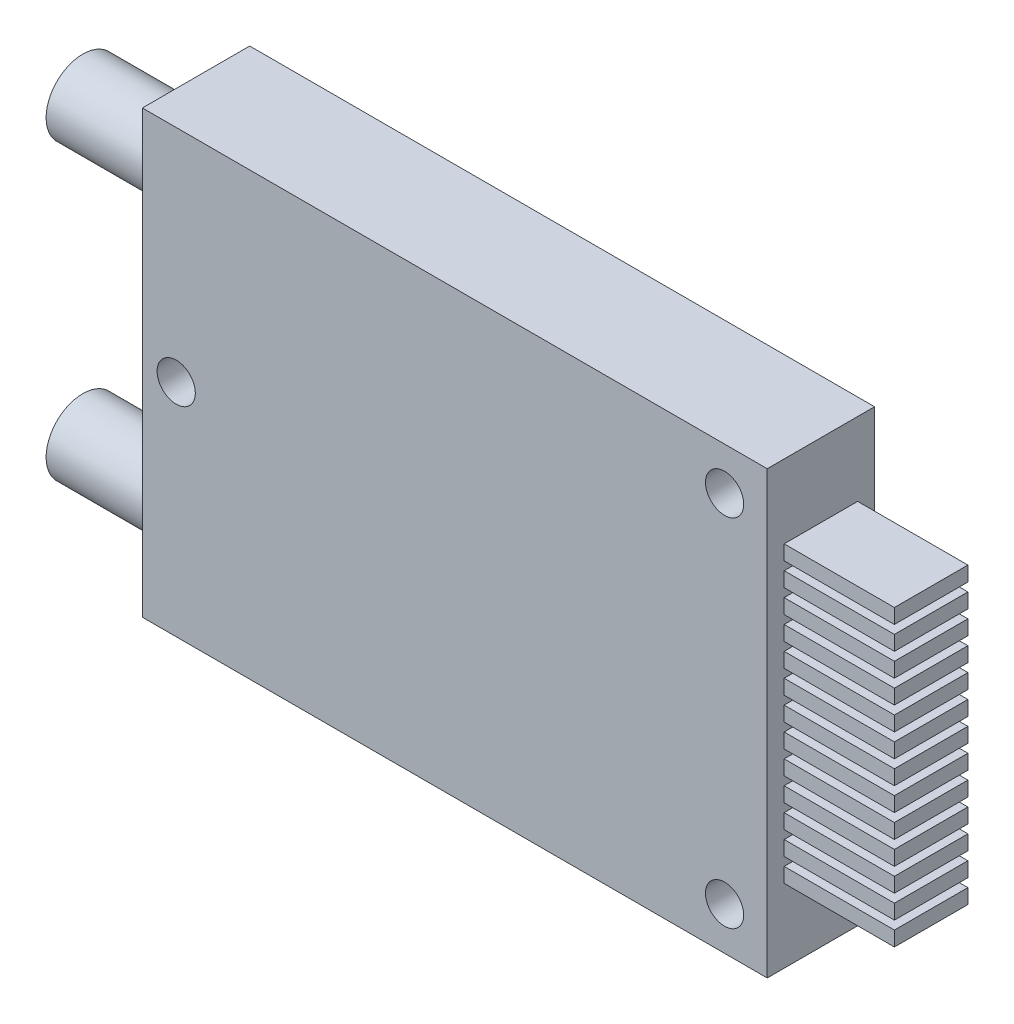
SolidWorks part; units mm, degrees
ref_plane "Front Plane" through (0, 0, 0) normal (0, 0, 1) x (1, 0, 0)
ref_plane "Top Plane" through (0, 0, 0) normal (0, 1, 0) x (1, 0, 0)
ref_plane "Right Plane" through (0, 0, 0) normal (1, 0, 0) x (0, 0, -1)
sketch "Sketch1" plane through (0, 0, 0) normal (0, 0, 1) x (1, 0, 0)
  line L1 (-21.25, 15) -> (21.25, 15)
  line L2 (-21.25, 15) -> (-21.25, -15)
  line L3 (-21.25, -15) -> (21.25, -15)
  line L4 (21.25, 15) -> (21.25, -15)
  point P4 (0, -15)
  point P5 (21.25, 0)
  dimension "D1" = 42.5
  dimension "D2" = 30
extrude "Boss-Extrude1" add sketch "Sketch1" along normal blind 7.3 contours L2 L3 L4 L1
sketch "Sketch2" plane through (0, 0, 7.3) normal (0, 0, 1) x (1, 0, 0)
  line L0 (-21.25, 15) -> (21.25, 15) construction
  line L1 (21.25, 15) -> (21.25, -15) construction
  line L2 (-21.25, -15) -> (21.25, -15) construction
  line L3 (-21.25, 15) -> (-21.25, -15) construction
  circle A0 centre (18.35, -12.1) radius 1.3
  circle A1 centre (18.35, 12.1) radius 1.3
  circle A2 centre (-18.95, 0) radius 1.3
  dimension "D1" = 2.6
  dimension "D2" = 2.9
  dimension "D3" = 2.9
  dimension "D4" = 2.9
  dimension "D5" = 2.9
  dimension "D6" = 2.3
  dimension "D7" = 15
extrude "Cut-Extrude1" cut sketch "Sketch2" against normal up to next
sketch "Sketch3" plane through (-21.25, 0, 0) normal (-1, 0, 0) x (0, 0, 1)
  line L0 (7.3, -15) -> (0, -15) construction
  line L1 (7.3, 15) -> (0, 15) construction
  circle A0 centre (3.65, 10) radius 2.5
  circle A1 centre (3.65, -10) radius 2.5
  point P8 (3.65, -15)
  dimension "D1" = 5
  dimension "D2" = 5
  dimension "D3" = 5
extrude "Boss-Extrude2" add sketch "Sketch3" along normal blind 7.7
sketch "Sketch4" plane through (21.25, 0, 0) normal (1, 0, 0) x (0, 0, -1)
  line L1 (-6.15, 10) -> (-1.15, 10)
  line L2 (-6.15, 10) -> (-6.15, 9)
  line L3 (-6.15, 9) -> (-1.15, 9)
  line L4 (-1.15, 10) -> (-1.15, 9)
  line L9 (-7.3, 15) -> (0, 15) construction
  line L10 (-6.15, 8.4167) -> (-1.15, 8.4167)
  line L11 (-6.15, 8.4167) -> (-6.15, 7.4167)
  line L12 (-6.15, 7.4167) -> (-1.15, 7.4167)
  line L13 (-1.15, 8.4167) -> (-1.15, 7.4167)
  line L14 (-6.15, 6.8333) -> (-1.15, 6.8333)
  line L15 (-6.15, 6.8333) -> (-6.15, 5.8333)
  line L16 (-6.15, 5.8333) -> (-1.15, 5.8333)
  line L17 (-1.15, 6.8333) -> (-1.15, 5.8333)
  line L18 (-6.15, 5.25) -> (-1.15, 5.25)
  line L19 (-6.15, 5.25) -> (-6.15, 4.25)
  line L20 (-6.15, 4.25) -> (-1.15, 4.25)
  line L21 (-1.15, 5.25) -> (-1.15, 4.25)
  line L22 (-6.15, 3.6667) -> (-1.15, 3.6667)
  line L23 (-6.15, 3.6667) -> (-6.15, 2.6667)
  line L24 (-6.15, 2.6667) -> (-1.15, 2.6667)
  line L25 (-1.15, 3.6667) -> (-1.15, 2.6667)
  line L26 (-6.15, 2.0833) -> (-1.15, 2.0833)
  line L27 (-6.15, 2.0833) -> (-6.15, 1.0833)
  line L28 (-6.15, 1.0833) -> (-1.15, 1.0833)
  line L29 (-1.15, 2.0833) -> (-1.15, 1.0833)
  line L30 (-6.15, 0.5) -> (-1.15, 0.5)
  line L31 (-6.15, 0.5) -> (-6.15, -0.5)
  line L32 (-6.15, -0.5) -> (-1.15, -0.5)
  line L33 (-1.15, 0.5) -> (-1.15, -0.5)
  line L34 (-6.15, -1.0833) -> (-1.15, -1.0833)
  line L35 (-6.15, -1.0833) -> (-6.15, -2.0833)
  line L36 (-6.15, -2.0833) -> (-1.15, -2.0833)
  line L37 (-1.15, -1.0833) -> (-1.15, -2.0833)
  line L38 (-6.15, -2.6667) -> (-1.15, -2.6667)
  line L39 (-6.15, -2.6667) -> (-6.15, -3.6667)
  line L40 (-6.15, -3.6667) -> (-1.15, -3.6667)
  line L41 (-1.15, -2.6667) -> (-1.15, -3.6667)
  line L42 (-6.15, -4.25) -> (-1.15, -4.25)
  line L43 (-6.15, -4.25) -> (-6.15, -5.25)
  line L44 (-6.15, -5.25) -> (-1.15, -5.25)
  line L45 (-1.15, -4.25) -> (-1.15, -5.25)
  line L46 (-6.15, -5.8333) -> (-1.15, -5.8333)
  line L47 (-6.15, -5.8333) -> (-6.15, -6.8333)
  line L48 (-6.15, -6.8333) -> (-1.15, -6.8333)
  line L49 (-1.15, -5.8333) -> (-1.15, -6.8333)
  line L50 (-6.15, -7.4167) -> (-1.15, -7.4167)
  line L51 (-6.15, -7.4167) -> (-6.15, -8.4167)
  line L52 (-6.15, -8.4167) -> (-1.15, -8.4167)
  line L53 (-1.15, -7.4167) -> (-1.15, -8.4167)
  line L54 (-6.15, -9) -> (-1.15, -9)
  line L55 (-6.15, -9) -> (-6.15, -10)
  line L56 (-6.15, -10) -> (-1.15, -10)
  line L57 (-1.15, -9) -> (-1.15, -10)
  line L58 (-7.3, -15) -> (0, -15) construction
  point P6 (-3.65, 15)
  point P9 (-3.65, 10)
  dimension "D1" = 5
  dimension "D2" = 1
  dimension "D3" = 5
  dimension "D5" = 5
  dimension "D4" = 13
extrude "Boss-Extrude3" add sketch "Sketch4" along normal blind 7.5
